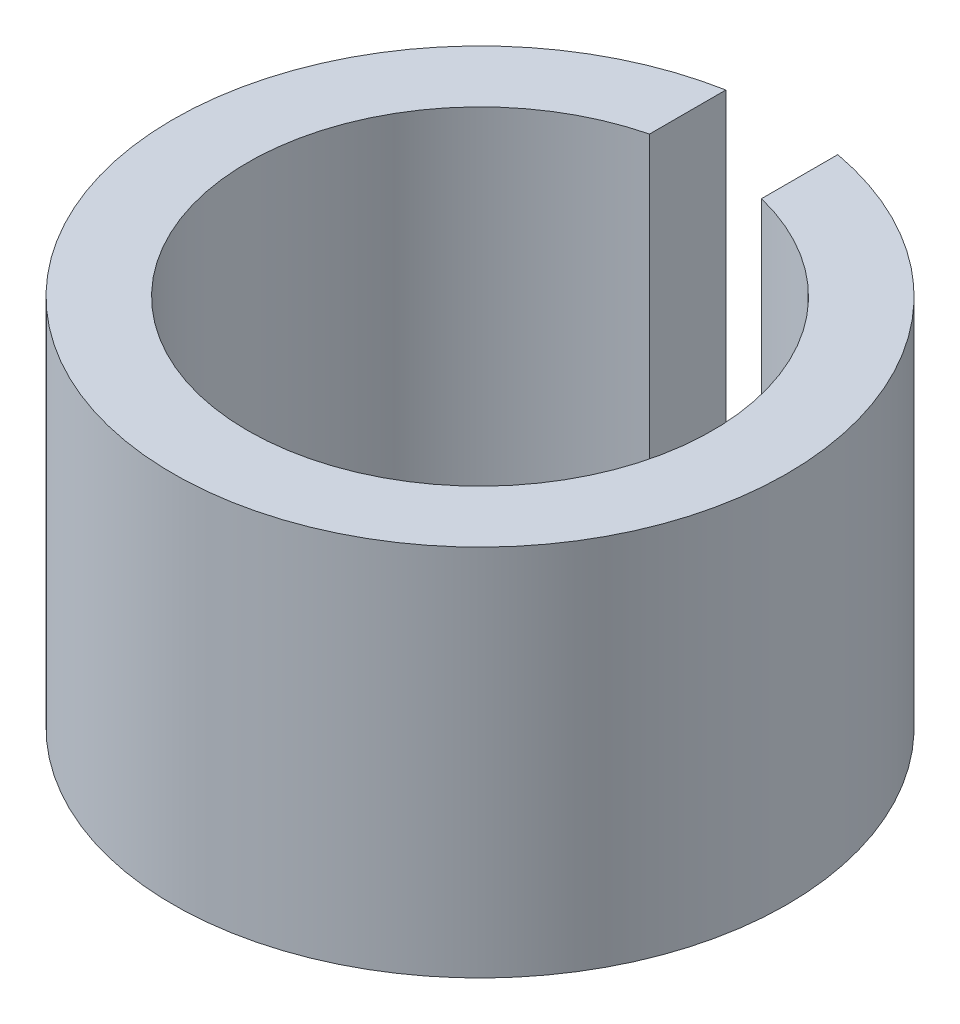
SolidWorks part; units mm, degrees
ref_plane "Front Plane" through (0, 0, 0) normal (0, 0, 1) x (1, 0, 0)
ref_plane "Top Plane" through (0, 0, 0) normal (0, 1, 0) x (1, 0, 0)
ref_plane "Right Plane" through (0, 0, 0) normal (1, 0, 0) x (0, 0, -1)
sketch "Sketch1" plane through (0, 0, 0) normal (0, 1, 0) x (1, 0, 0)
  line L3 (0, 0) -> (0, 5.6768) construction
  line L7 (-0.762, 4.1082) -> (-0.762, 3.0691)
  line L8 (0.762, 4.1082) -> (0.762, 3.0691)
  arc A0 (-0.762, 3.0691) -> (0.762, 3.0691) centre (0, 0) ccw
  arc A1 (-0.762, 4.1082) -> (0.762, 4.1082) centre (0, 0) ccw
  circle A2 centre (0, 0) radius 4.1783 construction
  circle A4 centre (0, 0) radius 3.1623 construction
  point P1 (-0.762, 3.5904)
  dimension "D1" = 6.3246
  dimension "D5" = 0.762
  dimension "D2" = 1.016
extrude "Boss-Extrude1" add sketch "Sketch1" along normal blind 5.08
